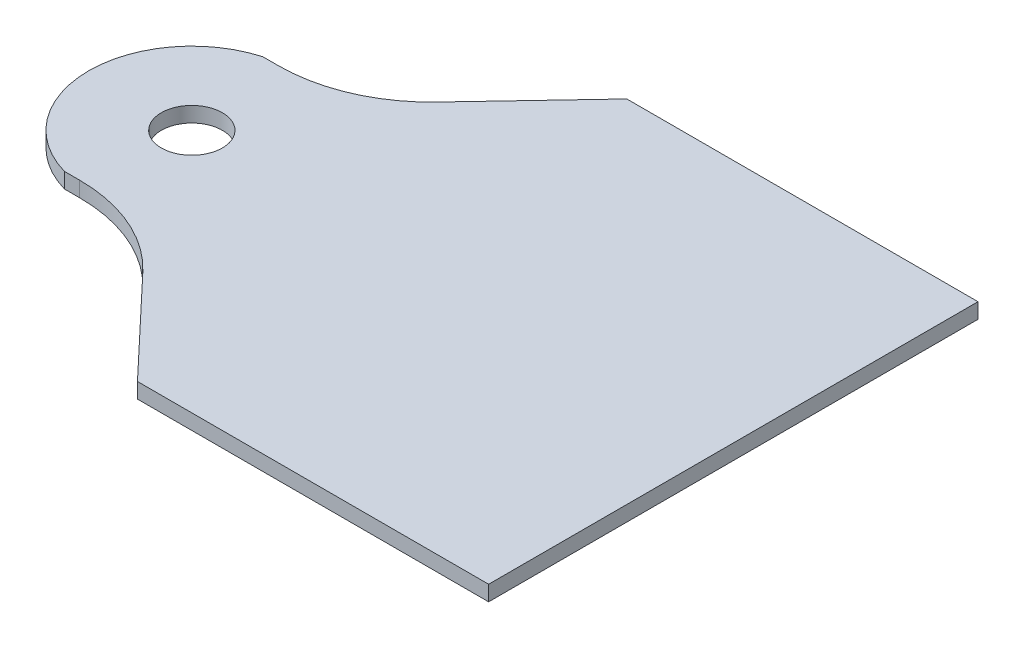
SolidWorks part; units mm, degrees
ref_plane "前视基准面" through (0, 0, 0) normal (0, 0, 1) x (1, 0, 0)
ref_plane "上视基准面" through (0, 0, 0) normal (0, 1, 0) x (1, 0, 0)
ref_plane "右视基准面" through (0, 0, 0) normal (1, 0, 0) x (0, 0, -1)
sketch "草图1" plane through (0, 0, 0) normal (0, 1, 0) x (1, 0, 0)
  line L0 (-49.6182, -13) -> (-51.6182, -13)
  line L1 (-23, -32.05) -> (23, -32.05)
  line L3 (-23, 32.05) -> (23, 32.05)
  line L4 (23, -32.05) -> (23, 32.05)
  line L5 (-23, -32.05) -> (23, 32.05) construction
  line L6 (-23, 32.05) -> (23, -32.05) construction
  line L10 (-35.0811, 19.2642) -> (-23, 32.05)
  line L11 (-35.0811, -19.2642) -> (-23, -32.05)
  line L13 (-49.6182, 13) -> (-51.6182, 13)
  arc A0 (-51.6182, 13) -> (-51.6182, -13) centre (-47.9273, 0) ccw
  circle A1 centre (-47.9273, 0) radius 4
  arc A2 (-35.0811, -19.2642) -> (-49.6182, -13) centre (-49.6182, -33) ccw
  arc A3 (-35.0811, 19.2642) -> (-49.6182, 13) centre (-49.6182, 33) cw
  point P0 (0, 0)
  point P5 (0, 0)
  point P6 (-145.3302, 0)
  point P8 (0, 13)
  point P9 (-145.3302, 13)
  point P10 (0, -13)
  point P11 (-145.3302, -13)
  point P16 (-59, 32.05)
  point P17 (-59, -37.2996)
  dimension "D3" = 8
  dimension "D4" = 20
  dimension "D1" = 64.1
  dimension "D2" = 46
  dimension "D5" = 2
  dimension "D6" = 2
extrude "凸台-拉伸1" add sketch "草图1" along normal blind 2
